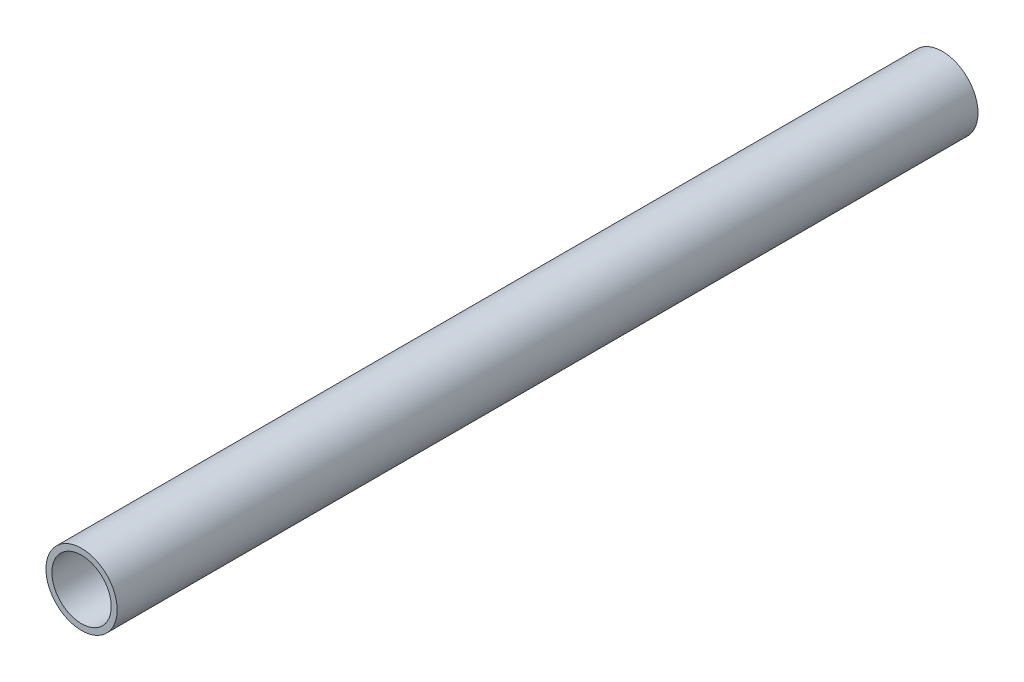
SolidWorks part; units mm, degrees
ref_plane "Front Plane" through (0, 0, 0) normal (0, 0, 1) x (1, 0, 0)
ref_plane "Top Plane" through (0, 0, 0) normal (0, 1, 0) x (1, 0, 0)
ref_plane "Right Plane" through (0, 0, 0) normal (1, 0, 0) x (0, 0, -1)
sketch "Sketch1" plane through (0, 0, 0) normal (0, 0, 1) x (1, 0, 0)
  circle A0 centre (-80, -58) radius 6
  circle A1 centre (-80, -58) radius 5
  dimension "D1" = 1
extrude "Boss-Extrude1" add sketch "Sketch1" along normal blind 145
